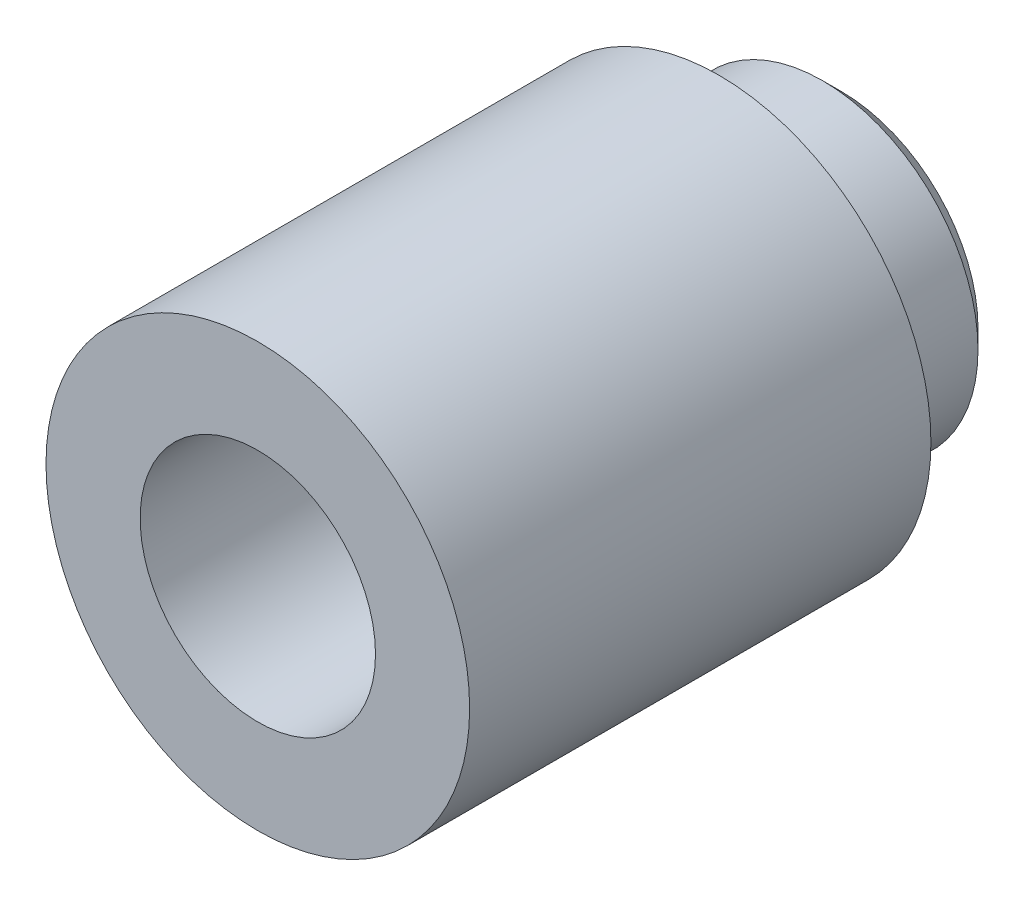
SolidWorks part; units mm, degrees
ref_plane "Front Plane" through (0, 0, 0) normal (0, 0, 1) x (1, 0, 0)
ref_plane "Top Plane" through (0, 0, 0) normal (0, 1, 0) x (1, 0, 0)
ref_plane "Right Plane" through (0, 0, 0) normal (1, 0, 0) x (0, 0, -1)
sketch "Sketch1" plane through (0, 0, 0) normal (0, 0, 1) x (1, 0, 0)
  circle A0 centre (0, 0) radius 2.25
  dimension "D1" = 4.5
extrude "Boss-Extrude1" add sketch "Sketch1" against normal blind 6.2
sketch "Sketch2" plane through (0, 0, -6.2) normal (0, 0, -1) x (-1, 0, 0)
  circle A0 centre (0, 0) radius 1.65
  dimension "D1" = 3.3
extrude "Cut-Extrude1" cut sketch "Sketch2" against normal blind 1.3 flip side to cut
sketch "Sketch3" plane through (0, 0, 0) normal (0, 0, 1) x (1, 0, 0)
  circle A0 centre (0, 0) radius 1.25
  dimension "D1" = 2.5
extrude "Cut-Extrude2" cut sketch "Sketch3" against normal through all
chamfer "Chamfer1" distance 0.2 angle 45 1 edges at (-1.65, 0, -6.2)
